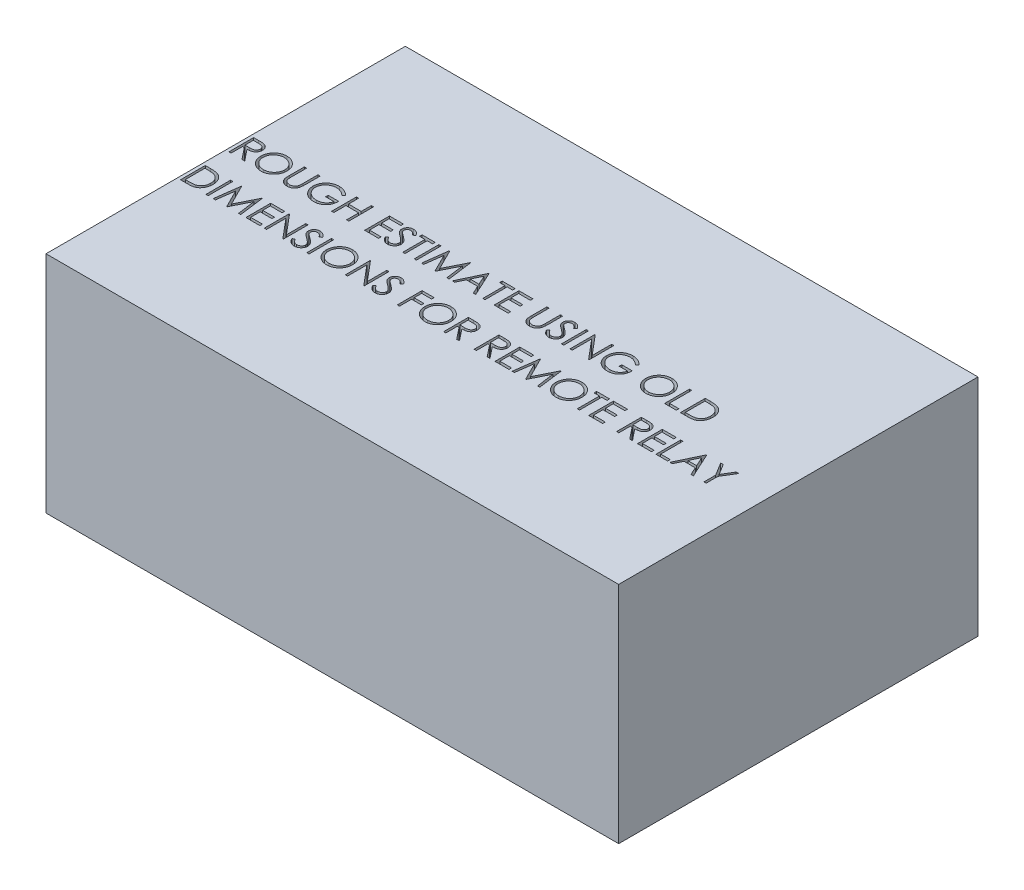
SolidWorks part; units mm, degrees
ref_plane "Front Plane" through (0, 0, 0) normal (0, 0, 1) x (1, 0, 0)
ref_plane "Top Plane" through (0, 0, 0) normal (0, 1, 0) x (1, 0, 0)
ref_plane "Right Plane" through (0, 0, 0) normal (1, 0, 0) x (0, 0, -1)
sketch "Sketch1" plane through (0, 0, 0) normal (0, 1, 0) x (1, 0, 0)
  line L1 (0, 0) -> (80.9625, 0)
  line L2 (0, 0) -> (0, 50.8)
  line L3 (0, 50.8) -> (80.9625, 50.8)
  line L4 (80.9625, 0) -> (80.9625, 50.8)
  dimension "D1" = 80.9625
  dimension "D2" = 50.8
extrude "Boss-Extrude1" add sketch "Sketch1" along normal blind 31.75
sketch "Sketch2" plane through (0, 31.75, 0) normal (0, 1, 0) x (1, 0, 0)
  line L0 (0, 25.4) -> (80.9625, 25.4) construction
  line L1 (0, 50.8) -> (0, 0) construction
  line L2 (80.9625, 0) -> (80.9625, 50.8) construction
  text T0 "ROUGH ESTIMATE USING OLD\r\nDIMENSIONS FOR REMOTE RELAY"
extrude "Cut-Extrude1" cut sketch "Sketch2" against normal blind 31.75
